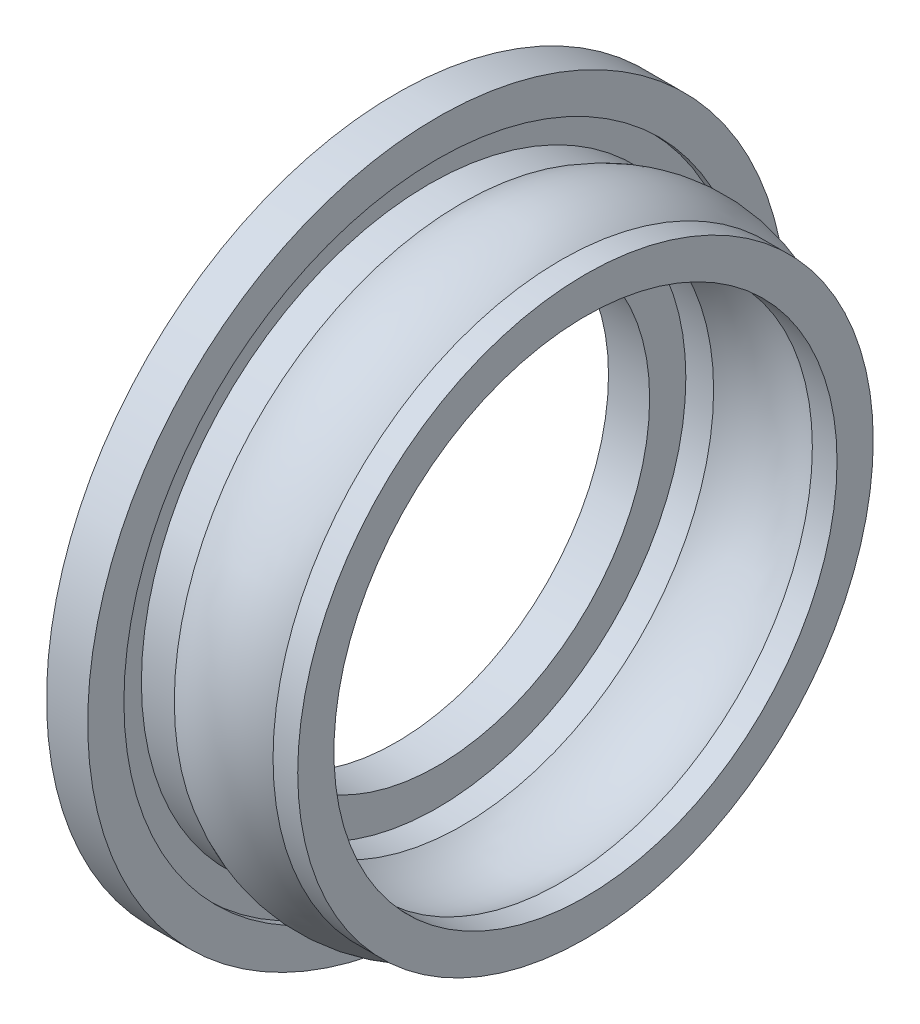
SolidWorks part; units mm, degrees
ref_plane "Front Plane" through (0, 0, 0) normal (0, 0, 1) x (1, 0, 0)
ref_plane "Top Plane" through (0, 0, 0) normal (0, 1, 0) x (1, 0, 0)
ref_plane "Right Plane" through (0, 0, 0) normal (1, 0, 0) x (0, 0, -1)
sketch "Sketch1" plane through (0, 0, 0) normal (1, 0, 0) x (0, 0, -1)
  circle A0 centre (0, 0) radius 17
  circle A1 centre (0, 0) radius 10.32
extrude "Boss-Extrude1" add sketch "Sketch1" along normal blind 2
sketch "Sketch4" plane through (0, 0, 0) normal (0, 1, 0) x (1, 0, 0)
  line L0 (9.2, 13.99) -> (9.2, 12.23)
  line L1 (2, 13.99) -> (2, 12.23)
  line L2 (2, 13.99) -> (9.2, 13.99) construction
  line L3 (2, 12.23) -> (9.2, 12.23) construction
  line L4 (2, 14.87) -> (9.2, 14.87) construction
  line L5 (8, 13.99) -> (9.2, 13.99)
  line L6 (2, 14.43) -> (9.2, 14.43) construction
  line L7 (2, 13.99) -> (3.2, 13.99)
  line L8 (2, 12.23) -> (3.2, 12.23)
  line L9 (8, 12.23) -> (9.2, 12.23)
  line L10 (2, 14.65) -> (9.2, 14.65) construction
  line L11 (9.2, 14.9841) -> (2, 14.9841) construction
  line L12 (2, -17) -> (2, 17) construction
  line L13 (9.2, 13.2241) -> (2, 13.2241) construction
  line L14 (2, 13.11) -> (9.2, 13.11) construction
  line L15 (2, 12.89) -> (9.2, 12.89) construction
  line L16 (2, 12.67) -> (9.2, 12.67) construction
  arc A1 (3.2, 13.99) -> (8, 13.99) centre (5.6, 9.9564) cw
  arc A2 (3.2, 12.23) -> (8, 12.23) centre (5.6, 8.1964) cw
  dimension "D2" = 0.66
  dimension "D1" = 0.44
  dimension "D3" = 1.76
  dimension "D4" = 1.76
ref_axis "Axis2" through (2, 0, 0) along (-1, 0, 0)
revolve "Revolve3" add sketch "Sketch4" angle 360 about axis through (2, 0, 0) along (-1, 0, 0)
sketch "Sketch5" plane through (2, 0, 0) normal (1, 0, 0) x (0, 0, -1)
  circle A2 centre (0, 0) radius 15.24
  circle A3 centre (0, 0) radius 13.99 construction
  circle A4 centre (0, 0) radius 13.99
extrude "Cut-Extrude1" cut sketch "Sketch5" against normal blind 0.4
sketch "Sketch6" plane through (2, 0, 0) normal (1, 0, 0) x (0, 0, -1)
  circle A1 centre (0, 0) radius 12.23 construction
  circle A2 centre (0, 0) radius 12.08
  circle A3 centre (0, 0) radius 12.08
  circle A4 centre (0, 0) radius 12.23
  dimension "D1" = 1.76
extrude "Cut-Extrude2" cut sketch "Sketch6" against normal blind 0.4
